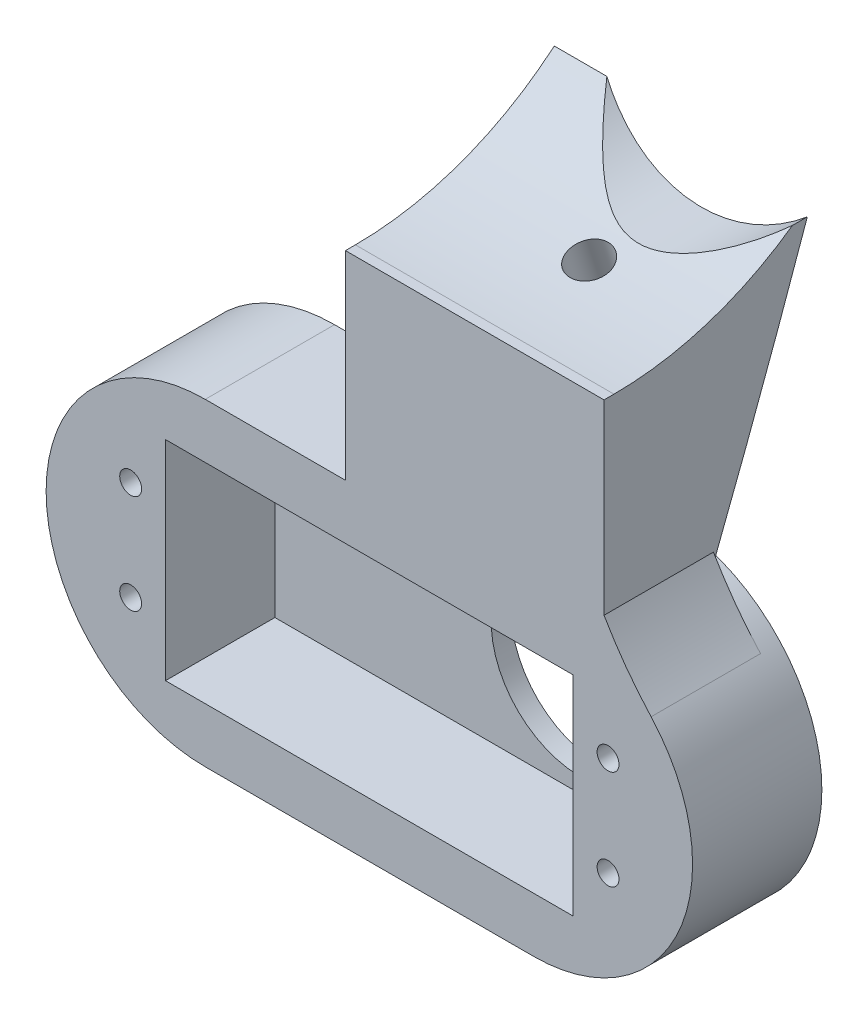
SolidWorks part; units mm, degrees
ref_plane "Front Plane" through (0, 0, 0) normal (0, 0, 1) x (1, 0, 0)
ref_plane "Top Plane" through (0, 0, 0) normal (0, 1, 0) x (1, 0, 0)
ref_plane "Right Plane" through (0, 0, 0) normal (1, 0, 0) x (0, 0, -1)
sketch "Sketch1" plane through (0, 0, 0) normal (0, 0, 1) x (1, 0, 0)
  line L0 (-3.5, 15.5) -> (-3.5, 5.5) construction
  line L1 (0, 0) -> (41, 0)
  line L2 (0, 0) -> (0, 21)
  line L3 (0, 21) -> (41, 21)
  line L4 (41, 0) -> (41, 21)
  line L5 (4, -5.5) -> (37, -5.5)
  line L6 (4, -5.5) -> (4, 26.5) construction
  line L7 (4, 26.5) -> (37, 26.5)
  line L8 (37, -5.5) -> (37, 26.5) construction
  arc A0 (37, -5.5) -> (37, 26.5) centre (37, 10.5) ccw
  arc A1 (4, 26.5) -> (4, -5.5) centre (4, 10.5) ccw
  circle A2 centre (-3.5, 15.5) radius 1.1
  circle A3 centre (-3.5, 5.5) radius 1.1
  circle A4 centre (44.5, 5.5) radius 1.1
  circle A5 centre (44.5, 15.5) radius 1.1
  point P9 (20.5, 26.5)
  point P10 (20.5, 21)
  point P11 (4, 10.5)
  point P12 (0, 10.5)
  point P23 (-3.5, 10.5)
  point P24 (0, 0)
  point P25 (0, 0)
  point P26 (0, 0)
  point P27 (0, 0)
  point P28 (0, 0)
  dimension "D6" = 2.2
  dimension "D1" = 21
  dimension "D2" = 41
  dimension "D3" = 33
  dimension "D4" = 32
  dimension "D5" = 10
  dimension "D7" = 3.5
  dimension "D8" = 3.5
extrude "Boss-Extrude1" add sketch "Sketch1" along normal blind 11
sketch "Sketch2" plane through (0, 0, 0) normal (0, 0, 1) x (1, 0, 0)
  line L0 (41, 0) -> (41, 21) construction
  line L1 (41, 0) -> (41, 21) construction
  line L2 (37, 26.5) -> (4, 26.5)
  line L3 (4, -5.5) -> (37, -5.5)
  line L4 (37, 26.5) -> (4, 26.5)
  line L5 (4, -5.5) -> (37, -5.5)
  line L6 (39.75, 10.5) -> (41, 10.5) construction
  circle A0 centre (30.75, 10.5) radius 9
  arc A2 (4, 26.5) -> (4, -5.5) centre (4, 10.5) ccw
  arc A3 (37, -5.5) -> (37, 26.5) centre (37, 10.5) ccw
  arc A4 (4, 26.5) -> (4, -5.5) centre (4, 10.5) ccw
  arc A5 (37, -5.5) -> (37, 26.5) centre (37, 10.5) ccw
  dimension "D2" = 18
  dimension "D3" = 1.25
  dimension "D1" = 0
extrude "Boss-Extrude2" add sketch "Sketch2" against normal blind 2
sketch "Sketch3" plane through (0, 0, 0) normal (0, 0, 1) x (1, 0, 0)
  line L0 (37, 26.5) -> (4, 26.5) construction
  line L1 (37, 26.5) -> (18.0959, 26.5)
  line L2 (53, 10.5) -> (-24.6881, 10.5) construction
  line L3 (44.0959, 46.5) -> (18.0959, 46.5)
  line L4 (18.0959, 46.5) -> (18.0959, 26.5)
  line L5 (44.0959, 46.5) -> (44.0959, 27.7449)
  arc A0 (37, -5.5) -> (37, 26.5) centre (37, 10.5) ccw construction
  arc A1 (48.8298, 21.2729) -> (37, 26.5) centre (37, 10.5) ccw
  arc A2 (44.0959, 27.7449) -> (48.8298, 21.2729) centre (76.5479, 46.5145) ccw
  dimension "D1" = 26
  dimension "D2" = 20
extrude "Boss-Extrude3" add sketch "Sketch3" along normal blind 10
sketch "Sketch5" plane through (44.0959, 0, 0) normal (1, 0, 0) x (0, 0, -1)
  line L0 (-10, 27.7449) -> (-10, 46.5) construction
  line L1 (0, 27.7449) -> (0, 46.5) construction
  line L2 (-10, 46.5) -> (0, 46.5) construction
  line L3 (-10, 27.7449) -> (-10, 46.5) construction
  line L4 (0, 26.738) -> (0, 46.5) construction
  line L5 (-10, 46.5) -> (0, 46.5) construction
  line L6 (-10, 46.5) -> (-10, 77.5) construction
  line L7 (-10, 77.5) -> (21, 77.5) construction
  line L8 (0, 26.738) -> (-10, 46.5)
  arc A0 (-10, 46.5) -> (21, 77.5) centre (-10, 77.5) ccw construction
  arc A1 (-10, 46.5) -> (10, 53.8146) centre (-10, 77.5) ccw
  spline S0 degree 2 poles (0, 26.738) (5.2637, 40.1813) (10, 53.8146) knots 0 0 0 1 1 1
  dimension "D1" = 62
  dimension "D2" = 20
extrude "Boss-Extrude4" add sketch "Sketch5" against normal up to surface (26 mm away) up to face at (18.0959, 36.5, 5)
sketch "Sketch6" plane through (0, 0, 0) normal (0, 0, 1) x (1, 0, 0)
  line L0 (18.0959, 53.8146) -> (18.0959, 46.5) construction
  line L1 (44.0959, 46.5) -> (44.0959, 53.8146) construction
  line L2 (18.0959, 53.8146) -> (44.0959, 53.8146) construction
  line L3 (44.0959, 46.5) -> (18.0959, 46.5) construction
  line L4 (18.0959, 53.8146) -> (18.0959, 46.5) construction
  line L5 (44.0959, 46.5) -> (44.0959, 53.8146) construction
  line L6 (18.0959, 53.8146) -> (44.0959, 53.8146) construction
  line L7 (44.0959, 46.5) -> (18.0959, 46.5) construction
  line L8 (34.5959, 48.9) -> (34.5959, 46.5) construction
  circle A0 centre (34.5959, 64.15) radius 15.25
  dimension "D1" = 30.5
  dimension "D2" = 2.4
  dimension "D3" = 16.5
extrude "Cut-Extrude1" cut sketch "Sketch6" against normal through all
ref_plane "Plane1" through (0, 23.3817, 7.5972) normal (0, -0.9511, -0.309) x (-1, 0, 0)
sketch "Sketch8" plane through (0, 23.3817, 7.5972) normal (0, -0.9511, -0.309) x (-1, 0, 0)
  circle A0 centre (-32.5621, 13.8804) radius 2
  dimension "D1" = 4
extrude "Cut-Extrude3" cut sketch "Sketch8" against normal through all both
ref_plane "Plane3" through (0, 33.3678, 10.8419) normal (0, -0.9511, -0.309) x (-1, 0, 0)
sketch "Sketch11" plane through (0, 33.3678, 10.8419) normal (0, -0.9511, -0.309) x (-1, 0, 0)
  circle A0 centre (-32.5621, 13.8804) radius 2 construction
  circle A1 centre (-32.5621, 13.8804) radius 2
  circle A2 centre (-32.5621, 13.8804) radius 3.875
  dimension "D1" = 7.75
extrude "Cut-Extrude4" cut sketch "Sketch11" along normal through all both 15.37
sketch "Sketch12" plane through (0, 0, 10) normal (0, 0, 1) x (1, 0, 0)
  line L4 (44.0959, 27.7449) -> (44.0959, 46.5)
  line L5 (44.0959, 46.5) -> (18.0959, 46.5)
  line L6 (18.0959, 46.5) -> (18.0959, 26.5)
  line L7 (18.0959, 26.5) -> (37, 26.5)
  line L8 (44.0959, 27.7449) -> (44.0959, 46.5)
  line L9 (44.0959, 46.5) -> (18.0959, 46.5)
  line L10 (18.0959, 46.5) -> (18.0959, 26.5)
  line L11 (18.0959, 26.5) -> (37, 26.5)
  arc A2 (48.8298, 21.2729) -> (37, 26.5) centre (37, 10.5) ccw
  arc A3 (44.0959, 27.7449) -> (48.8298, 21.2729) centre (76.5479, 46.5145) ccw
  arc A4 (48.8298, 21.2729) -> (37, 26.5) centre (37, 10.5) ccw
  arc A5 (44.0959, 27.7449) -> (48.8298, 21.2729) centre (76.5479, 46.5145) ccw
  dimension "D1" = 0
extrude "Boss-Extrude6" add sketch "Sketch12" along normal up to surface (1 mm away) up to face at (45.6, 5.5, 11)
